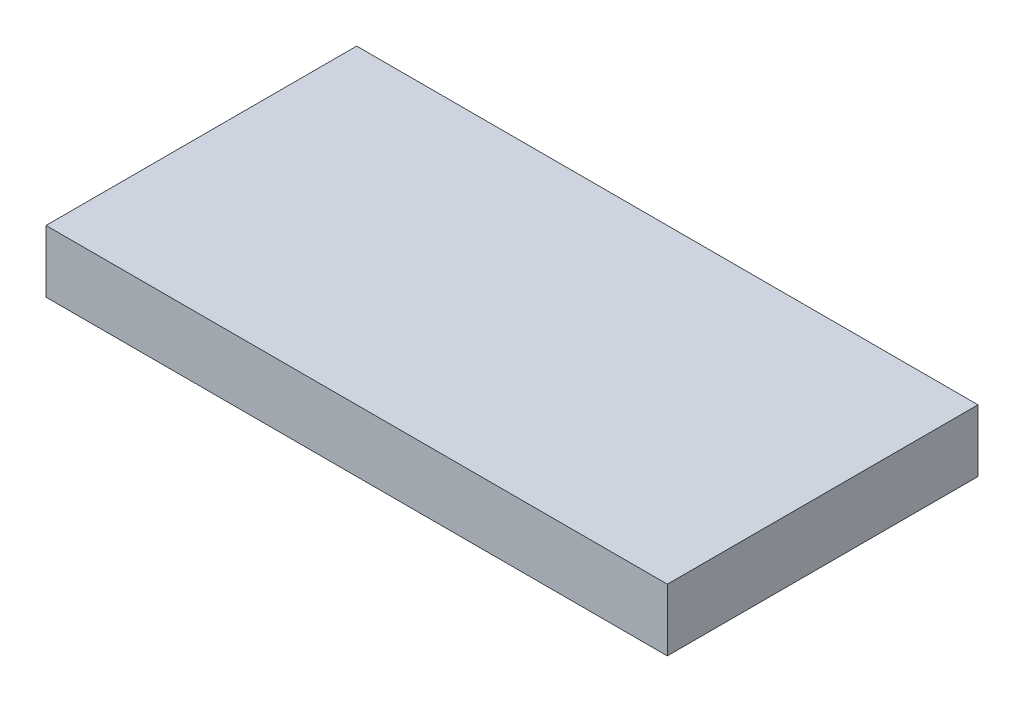
SolidWorks part; units mm, degrees
ref_plane "Front" through (0, 0, 0) normal (0, 0, 1) x (1, 0, 0)
ref_plane "Top" through (0, 0, 0) normal (0, 1, 0) x (1, 0, 0)
ref_plane "Right" through (0, 0, 0) normal (1, 0, 0) x (0, 0, -1)
sketch "草图1" plane through (0, 0, 0) normal (0, 1, 0) x (1, 0, 0)
  line L1 (-50, -25) -> (50, -25)
  line L2 (-50, -25) -> (-50, 25)
  line L3 (-50, 25) -> (50, 25)
  line L4 (50, -25) -> (50, 25)
  line L5 (-50, -25) -> (50, 25) construction
  line L6 (-50, 25) -> (50, -25) construction
  point P0 (0, 0)
  dimension "L" = 100
  dimension "W" = 50
extrude "凸台-拉伸1" add sketch "草图1" along normal blind 10
